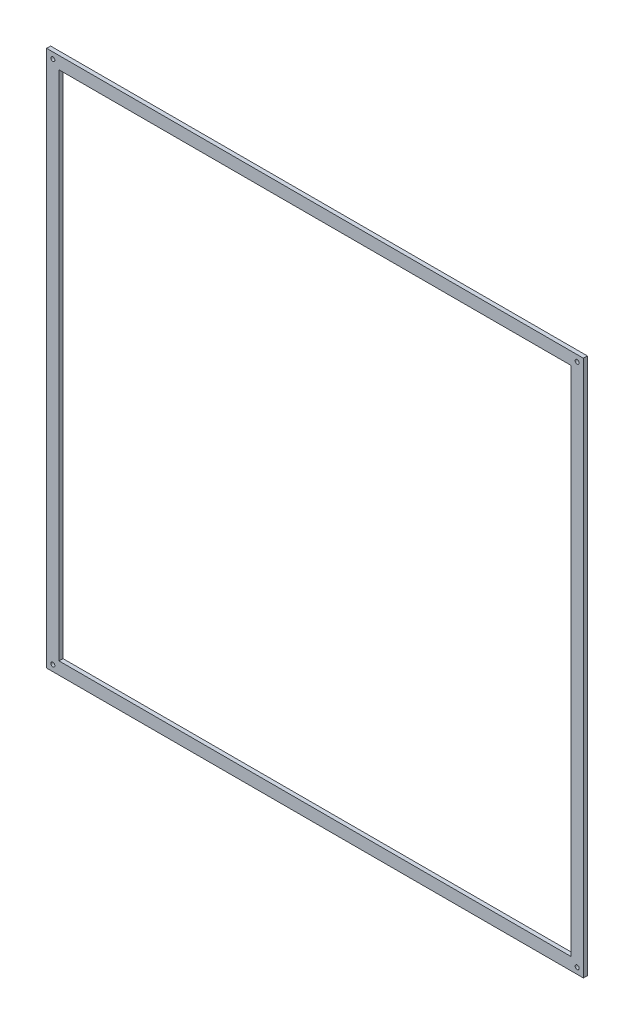
SolidWorks part; units mm, degrees
ref_plane "Front Plane" through (0, 0, 0) normal (0, 0, 1) x (1, 0, 0)
ref_plane "Top Plane" through (0, 0, 0) normal (0, 1, 0) x (1, 0, 0)
ref_plane "Right Plane" through (0, 0, 0) normal (1, 0, 0) x (0, 0, -1)
sketch "Sketch1" plane through (0, 0, 0) normal (0, 0, 1) x (1, 0, 0)
  line L1 (656.1951, 656.1951) -> (-656.1951, 656.1951) construction
  line L2 (-656.1951, 656.1951) -> (-656.1951, -656.1951) construction
  line L3 (-656.1951, -656.1951) -> (656.1951, -656.1951) construction
  line L4 (656.1951, -656.1951) -> (656.1951, 656.1951) construction
  line L5 (-671.7514, -671.7514) -> (671.7514, -671.7514)
  line L6 (671.7514, -671.7514) -> (671.7514, 671.7514)
  line L7 (671.7514, 671.7514) -> (-671.7514, 671.7514)
  line L8 (-671.7514, 671.7514) -> (-671.7514, -671.7514)
  line L9 (-640.6387, -640.6387) -> (640.6387, -640.6387)
  line L10 (640.6387, -640.6387) -> (640.6387, 640.6387)
  line L11 (640.6387, 640.6387) -> (-640.6387, 640.6387)
  line L12 (-640.6387, 640.6387) -> (-640.6387, -640.6387)
  circle A0 centre (0, 0) radius 928 construction
  circle A1 centre (-656.1951, 656.1951) radius 5
  circle A2 centre (656.1951, 656.1951) radius 5
  circle A3 centre (656.1951, -656.1951) radius 5
  circle A4 centre (-656.1951, -656.1951) radius 5
  circle A5 centre (0, 0) radius 950 construction
  circle A6 centre (0, 0) radius 906 construction
  point P17 (0, 0)
  dimension "D1" = 4
extrude "Boss-Extrude1" add sketch "Sketch1" along normal blind 10
